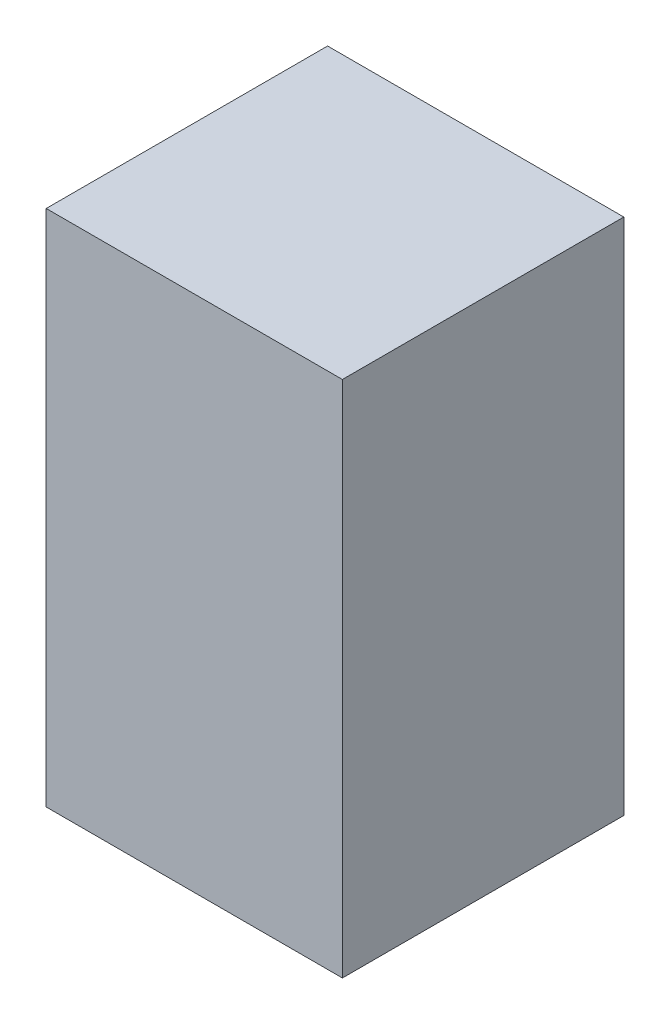
SolidWorks part; units mm, degrees
ref_plane "Front Plane" through (0, 0, 0) normal (0, 0, 1) x (1, 0, 0)
ref_plane "Top Plane" through (0, 0, 0) normal (0, 1, 0) x (1, 0, 0)
ref_plane "Right Plane" through (0, 0, 0) normal (1, 0, 0) x (0, 0, -1)
sketch "Sketch1" plane through (0, 0, 0) normal (0, 0, 1) x (1, 0, 0)
  line L1 (0, 0) -> (25.4, 0)
  line L2 (0, 0) -> (0, 44.45)
  line L3 (0, 44.45) -> (25.4, 44.45)
  line L4 (25.4, 0) -> (25.4, 44.45)
  dimension "D1" = 44.45
  dimension "D2" = 25.4
extrude "Boss-Extrude1" add sketch "Sketch1" along normal blind 24.13
